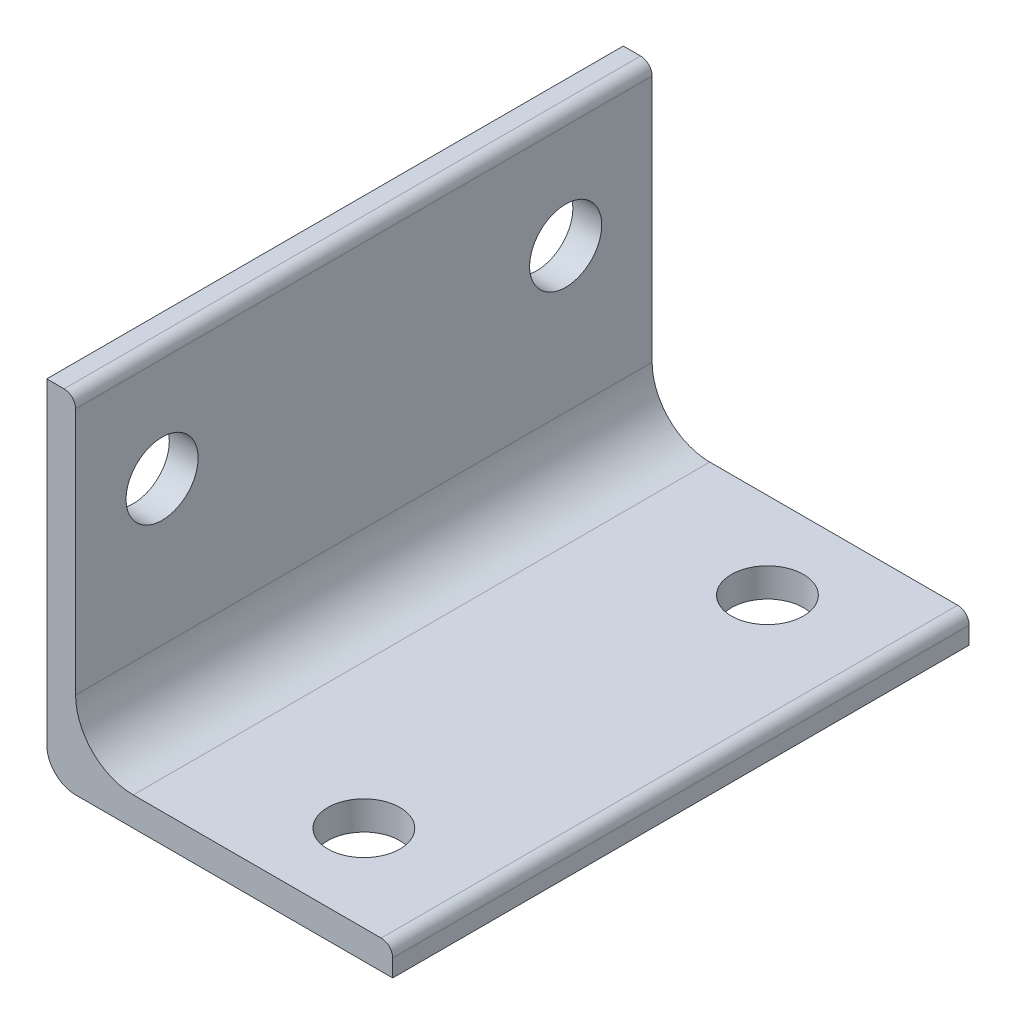
SolidWorks part; units mm, degrees
material "Plain Carbon Steel"
ref_plane "Front" through (0, 0, 0) normal (0, 0, 1) x (1, 0, 0)
ref_plane "Top" through (0, 0, 0) normal (0, 1, 0) x (1, 0, 0)
ref_plane "Right" through (0, 0, 0) normal (1, 0, 0) x (0, 0, -1)
sketch "Sketch1" plane through (0, 0, 0) normal (0, 0, 1) x (1, 0, 0)
  line L0 (0, 0) -> (0, 34.925)
  line L1 (0, 34.925) -> (-3.175, 34.925)
  line L2 (-3.175, 34.925) -> (-3.175, -3.175)
  line L3 (-3.175, -3.175) -> (34.925, -3.175)
  line L4 (34.925, -3.175) -> (34.925, 0)
  line L5 (34.925, 0) -> (0, 0)
  dimension "Height" = 38.1
  dimension "Width" = 38.1
  dimension "Wall Thickness" = 3.175
sketch "Sketch2" plane through (0, 0, 0) normal (1, 0, 0) x (0, 0, -1)
  line L0 (-152.4, 0) -> (152.4, 0) construction
  line L1 (152.4, -3.175) -> (-152.4, -3.175) construction
  point P2 (0, 0)
  point P3 (0, -3.175)
  point P5 (152.4, 0)
  point P9 (0, -3.175)
  point P10 (-152.4, -3.175)
  point P11 (152.4, -3.175)
  point P12 (-152.4, 0)
  dimension "Length" = 304.8
sketch "Sketch3" plane through (0, 0, 0) normal (0, 0, 1) x (1, 0, 0)
  line L0 (0, 0) -> (0, 34.925) construction
  line L1 (0, 34.925) -> (-3.175, 34.925) construction
  line L2 (-3.175, 34.925) -> (-3.175, -3.175) construction
  line L3 (-3.175, -3.175) -> (34.925, -3.175) construction
  line L4 (34.925, -3.175) -> (34.925, 0) construction
  line L5 (34.925, 0) -> (0, 0) construction
  line L6 (0, 6.35) -> (0, 33.655)
  line L7 (-1.27, 34.925) -> (-3.175, 34.925)
  line L8 (-3.175, 34.925) -> (-3.175, 0)
  line L9 (0, -3.175) -> (34.925, -3.175)
  line L10 (34.925, -3.175) -> (34.925, -1.27)
  line L11 (33.655, 0) -> (6.35, 0)
  arc A0 (0, 6.35) -> (6.35, 0) centre (6.35, 6.35) ccw
  arc A1 (34.925, -1.27) -> (33.655, 0) centre (33.655, -1.27) ccw
  arc A2 (0, 33.655) -> (-1.27, 34.925) centre (-1.27, 33.655) ccw
  arc A3 (-3.175, 0) -> (0, -3.175) centre (0, 0) ccw
  dimension "D1" = 1.27
  dimension "D2" = 6.35
extrude "Boss-Extrude1" add sketch "Sketch3" along normal blind 63.5
hole_wizard "5/16 (0.3125) Diameter Hole1" positions "3DSketch1" profile "Sketch4" hole size "5/16" standard "ANSI Inch" end condition through all
sketch3d "3DSketch1"
  line L0 (33.655, 0, 63.5) -> (6.35, 0, 63.5) construction
  line L1 (33.655, 0, 0) -> (6.35, 0, 0) construction
  line L2 (33.655, 0, 63.5) -> (33.655, 0, 0) construction
  line L3 (0, 33.655, 63.5) -> (0, 33.655, 0) construction
  line L4 (0, 6.35, 63.5) -> (0, 33.655, 63.5) construction
  line L5 (0, 6.35, 0) -> (0, 33.655, 0) construction
  point P0 (22.225, 0, 53.975)
  point P2 (22.225, 0, 9.525)
  point P4 (0, 22.225, 9.525)
  point P6 (0, 22.225, 53.975)
  dimension "D1" = 9.525
  dimension "D2" = 9.525
  dimension "D3" = 11.43
  dimension "D4" = 11.43
  dimension "D5" = 9.525
  dimension "D6" = 9.525
sketch "Sketch4" plane through (22.225, 0, 53.975) normal (1, 0, 0) x (0, 0, 1)
  line L0 (0, 0) -> (0, 3.175)
  line L1 (0, 3.175) -> (3.9687, 3.175)
  line L2 (3.9687, 3.175) -> (3.9688, 0)
  line L5 (3.9688, 0) -> (0, 0)
  line L11 (0, -6.35) -> (0, 107.95) construction
  dimension "Thru Hole Dia." = 7.9375
  dimension "Thru Hole Depth" = 3.175
equation "\"D1@Sketch3\"=\"Wall Thickness@Sketch1\"*0.4"
equation "\"D2@Sketch3\"=\"Wall Thickness@Sketch1\"*2"
